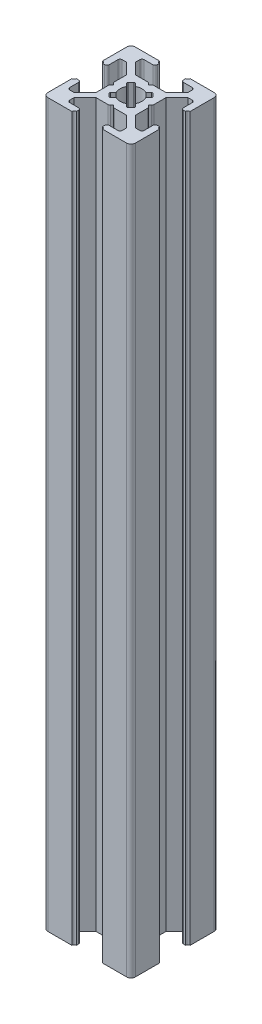
SolidWorks part; units mm, degrees
ref_plane "Front Plane" through (0, 0, 0) normal (0, 0, 1) x (1, 0, 0)
ref_plane "Top Plane" through (0, 0, 0) normal (0, 1, 0) x (1, 0, 0)
ref_plane "Right Plane" through (0, 0, 0) normal (1, 0, 0) x (0, 0, -1)
sketch "Sketch3" plane through (0, 0, 0) normal (0, 1, 0) x (1, 0, 0)
  line L0 (7, 20) -> (7, 18.5)
  line L1 (0, 0) -> (20, 0)
  line L2 (0, 0) -> (0, 20)
  line L3 (0, 20) -> (20, 20)
  line L4 (20, 0) -> (20, 20)
  line L5 (7, 18.5) -> (4, 18.5)
  line L6 (4, 18.5) -> (4, 17)
  line L7 (4, 17) -> (6.5, 14.5)
  line L8 (6.5, 14.5) -> (13.5, 14.5)
  line L9 (13.5, 14.5) -> (16, 17)
  line L10 (16, 17) -> (16, 18.5)
  line L11 (16, 18.5) -> (13, 18.5)
  line L12 (13, 18.5) -> (13, 20)
  line L13 (13, 20) -> (7, 20)
  line L14 (9.5, 14.5) -> (10, 14)
  line L15 (10, 14) -> (10.5, 14.5)
  line L16 (10.5, 14.5) -> (9.5, 14.5)
  line L17 (13, 19.5) -> (13, 20)
  line L18 (13.5, 20) -> (13, 20)
  line L19 (7, 19.5) -> (7, 20)
  line L20 (6.5, 20) -> (7, 20)
  line L21 (0, 13) -> (1.5, 13)
  line L22 (1.5, 13) -> (1.5, 16)
  line L23 (1.5, 16) -> (3, 16)
  line L24 (3, 16) -> (5.5, 13.5)
  line L25 (5.5, 13.5) -> (5.5, 6.5)
  line L26 (5.5, 6.5) -> (3, 4)
  line L27 (3, 4) -> (1.5, 4)
  line L28 (1.5, 4) -> (1.5, 7)
  line L29 (1.5, 7) -> (0, 7)
  line L30 (0, 7) -> (0, 13)
  line L31 (5.5, 10.5) -> (5.5, 9.5)
  line L32 (5.5, 9.5) -> (6, 10)
  line L33 (6, 10) -> (5.5, 10.5)
  line L34 (0.5, 13) -> (0, 13)
  line L35 (0, 13.5) -> (0, 13)
  line L36 (0, 6.5) -> (0, 7)
  line L37 (0.5, 7) -> (0, 7)
  line L38 (10, 20) -> (10, 0) construction
  line L39 (20, 10) -> (0, 10) construction
  line L40 (10, 6) -> (10.5, 5.5)
  line L41 (9.5, 5.5) -> (10, 6)
  line L42 (10.5, 5.5) -> (9.5, 5.5)
  line L43 (13.5, 0) -> (13, 0)
  line L44 (13, 0.5) -> (13, 0)
  line L45 (6.5, 0) -> (7, 0)
  line L46 (7, 0.5) -> (7, 0)
  line L47 (13, 1.5) -> (13, 0)
  line L48 (16, 1.5) -> (13, 1.5)
  line L49 (16, 3) -> (16, 1.5)
  line L50 (13.5, 5.5) -> (16, 3)
  line L51 (6.5, 5.5) -> (13.5, 5.5)
  line L52 (4, 3) -> (6.5, 5.5)
  line L53 (4, 1.5) -> (4, 3)
  line L54 (7, 1.5) -> (4, 1.5)
  line L55 (7, 0) -> (7, 1.5)
  line L56 (13, 0) -> (7, 0)
  line L57 (14.5, 9.5) -> (14, 10)
  line L58 (14.5, 10.5) -> (14.5, 9.5)
  line L59 (14, 10) -> (14.5, 10.5)
  line L60 (19.5, 7) -> (20, 7)
  line L61 (20, 6.5) -> (20, 7)
  line L62 (20, 13.5) -> (20, 13)
  line L63 (19.5, 13) -> (20, 13)
  line L64 (18.5, 7) -> (20, 7)
  line L65 (18.5, 4) -> (18.5, 7)
  line L66 (17, 4) -> (18.5, 4)
  line L67 (14.5, 6.5) -> (17, 4)
  line L68 (14.5, 13.5) -> (14.5, 6.5)
  line L69 (17, 16) -> (14.5, 13.5)
  line L70 (18.5, 16) -> (17, 16)
  line L71 (18.5, 13) -> (18.5, 16)
  line L72 (20, 13) -> (18.5, 13)
  line L73 (20, 7) -> (20, 13)
  arc A0 (13.5, 20) -> (13, 19.5) centre (13, 20) cw
  arc A1 (6.5, 20) -> (7, 19.5) centre (7, 20) ccw
  arc A2 (0.5, 13) -> (0, 13.5) centre (0, 13) ccw
  arc A3 (0.5, 7) -> (0, 6.5) centre (0, 7) cw
  arc A4 (13.5, 0) -> (13, 0.5) centre (13, 0) ccw
  arc A5 (6.5, 0) -> (7, 0.5) centre (7, 0) cw
  arc A6 (19.5, 7) -> (20, 6.5) centre (20, 7) ccw
  arc A7 (19.5, 13) -> (20, 13.5) centre (20, 13) cw
  point P7 (10, 14.5)
  point P16 (10, 20)
  point P26 (5.5, 10)
  point P35 (0, 10)
  dimension "D16" = 0.5
  dimension "D17" = 0.5
  dimension "D28" = 0.5
  dimension "D29" = 0.5
  dimension "D1" = 20
  dimension "D2" = 20
  dimension "D3" = 7
  dimension "D4" = 7
  dimension "D5" = 1.5
  dimension "D6" = 1.5
  dimension "D7" = 3
  dimension "D8" = 3
  dimension "D9" = 1.5
  dimension "D10" = 1.5
  dimension "D11" = 7
  dimension "D12" = 5.5
  dimension "D13" = 0.5
  dimension "D14" = 0.5
  dimension "D15" = 0.5
  dimension "D18" = 7
  dimension "D19" = 7
  dimension "D20" = 1.5
  dimension "D21" = 1.5
  dimension "D22" = 3
  dimension "D23" = 7
  dimension "D24" = 5.5
  dimension "D25" = 0.5
  dimension "D26" = 0.5
  dimension "D27" = 0.5
extrude "Boss-Extrude1" add sketch "Sketch3" along normal blind 165 contours L72 A7 L4 L3 A0 L12 L11 L10 L9 L8 L15 L14 L7 L6 L5 L0 A1 L2 A2 L21 L22 L23 L24 L25 L33 L32 L26 L27 L28 L29 A3 L1 A5 L55 L54 L53 L52 L51 L41 L40 L50 L49 L48 L47 A4
fillet "Fillet1" radius 1 4 edges at (0, 82.5, 0) (20, 82.5, 0) (20, 82.5, -20) (0, 82.5, -20)
sketch "Sketch4" plane through (0, 165, 0) normal (0, 1, 0) x (1, 0, 0)
  line L0 (13.5, 14.5) -> (5.5, 6.5) construction
  line L1 (14.5, 13.5) -> (6.5, 5.5) construction
  line L2 (10.5, 14.5) -> (14.5, 10.5) construction
  line L3 (12, 13) -> (13, 12)
  line L4 (13, 12) -> (8, 7)
  line L5 (8, 7) -> (7, 8)
  line L6 (7, 8) -> (12, 13)
  line L7 (13.5, 14.5) -> (16, 17) construction
  line L8 (17, 16) -> (14.5, 13.5) construction
  line L9 (5.5, 9.5) -> (9.5, 5.5) construction
  line L10 (5.5, 10.5) -> (9.5, 14.5) construction
  line L11 (14.5, 9.5) -> (10.5, 5.5) construction
  line L12 (6.5, 14.5) -> (14.5, 6.5) construction
  line L13 (5.5, 13.5) -> (13.5, 5.5) construction
  line L14 (7, 12) -> (8, 13)
  line L15 (8, 13) -> (13, 8)
  line L16 (13, 8) -> (12, 7)
  line L17 (12, 7) -> (7, 12)
  line L18 (4, 17) -> (6.5, 14.5) construction
  line L19 (3, 16) -> (5.5, 13.5) construction
  line L20 (20, 10) -> (0, 10) construction
  circle A0 centre (10, 10) radius 2.5
  dimension "D1" = 5
extrude "Cut-Extrude1" cut sketch "Sketch4" against normal through all contours L6 A0 L15 | L4 A0 L6 L15 | L15 A0 L17 L6 | L17 L4 L15 L6 | L17 A0 L6 | L6 A0 L4 L17 | L4 A0 L17 | L17 A0 L15 L4 | L15 A0 L4 | A0 L6 L5 L4 | A0 L17 L16 L15 | A0 L4 L3 L6 | A0 L15 L14 L17
fillet "Fillet2" radius 0.5 24 edges at (1.5, 82.5, -16) (1.5, 82.5, -13) (5.5, 82.5, -10.5) (5.5, 82.5, -9.5) (1.5, 82.5, -7) (1.5, 82.5, -4) (4, 82.5, -1.5) (7, 82.5, -1.5) (9.5, 82.5, -5.5) (10.5, 82.5, -5.5) (13, 82.5, -1.5) (16, 82.5, -1.5) (18.5, 82.5, -4) (18.5, 82.5, -7) (18.5, 82.5, -13) (18.5, 82.5, -16) (14.5, 82.5, -9.5) (14.5, 82.5, -10.5) (10.5, 82.5, -14.5) (9.5, 82.5, -14.5) (16, 82.5, -18.5) (13, 82.5, -18.5) (7, 82.5, -18.5) (4, 82.5, -18.5)
fillet "Fillet3" radius 0.25 8 edges at (13, 82.5, -8) (12, 82.5, -7) (13, 82.5, -12) (12, 82.5, -13) (8, 82.5, -13) (7, 82.5, -12) (7, 82.5, -8) (8, 82.5, -7)
